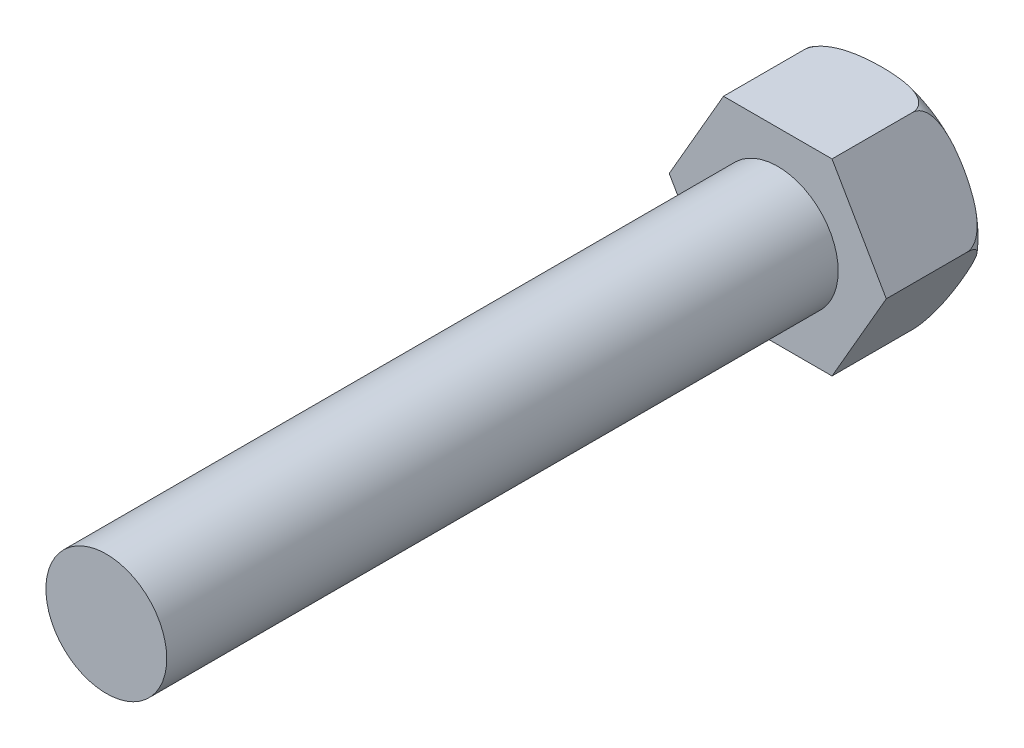
SolidWorks part; units mm, degrees
ref_plane "Front Plane" through (0, 0, 0) normal (0, 0, 1) x (1, 0, 0)
ref_plane "Top Plane" through (0, 0, 0) normal (0, 1, 0) x (1, 0, 0)
ref_plane "Right Plane" through (0, 0, 0) normal (1, 0, 0) x (0, 0, -1)
sketch "Sketch1" plane through (0, 0, 0) normal (0, 0, 1) x (1, 0, 0)
  line L1 (-4.0415, 0) -> (-2.0207, -3.5)
  line L2 (-2.0207, -3.5) -> (2.0207, -3.5)
  line L3 (2.0207, -3.5) -> (4.0415, 0)
  line L4 (4.0415, 0) -> (2.0207, 3.5)
  line L5 (2.0207, 3.5) -> (-2.0207, 3.5)
  line L6 (-2.0207, 3.5) -> (-4.0415, 0)
  circle A0 centre (0, 0) radius 3.5 construction
  point P1 (0, 0)
  dimension "D1" = 7
extrude "Boss-Extrude1" add sketch "Sketch1" along normal blind 4
sketch "Sketch2" plane through (0, 0, 4) normal (0, 0, 1) x (1, 0, 0)
  circle A0 centre (0, 0) radius 2.25
  dimension "D1" = 4.5
extrude "Boss-Extrude2" add sketch "Sketch2" along normal blind 25
sketch "Sketch3" plane through (0, 0, 0) normal (0, 1, 0) x (1, 0, 0)
  line L0 (4.0415, 0) -> (2.0207, 0) construction
  line L1 (4.0415, -4) -> (4.0415, 0) construction
  line L2 (3.0415, 0) -> (4.0415, 0)
  line L3 (4.0415, 0) -> (4.0415, -1)
  arc A0 (3.0415, 0) -> (4.0415, -1) centre (3.0415, -1) cw
  dimension "D1" = 1
revolve "Cut-Revolve1" cut sketch "Sketch3" angle 360 about axis through (0, 0, 29) along (0, 0, -1)
